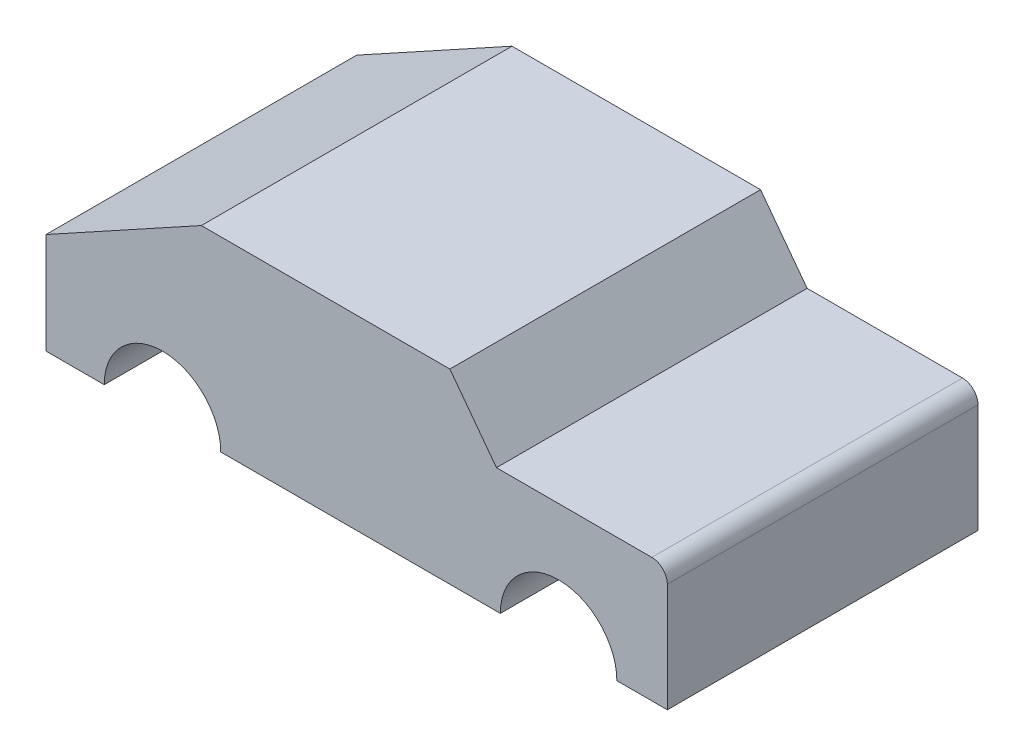
SolidWorks part; units mm, degrees
ref_plane "Front Plane" through (0, 0, 0) normal (0, 0, 1) x (1, 0, 0)
ref_plane "Top Plane" through (0, 0, 0) normal (0, 1, 0) x (1, 0, 0)
ref_plane "Right Plane" through (0, 0, 0) normal (1, 0, 0) x (0, 0, -1)
sketch "Sketch2" plane through (0, 0, 0) normal (0, 0, 1) x (1, 0, 0)
  line L0 (332.0819, 10.1189) -> (232.0819, 65.1189)
  line L2 (-67.9181, 15.1189) -> (-67.9181, -54.8811)
  line L3 (-67.9181, -54.8811) -> (-35.4181, -54.8811)
  line L4 (332.0819, 10.1189) -> (332.0819, -54.8811)
  line L5 (232.0819, 65.1189) -> (72.0819, 65.1189)
  line L6 (72.0819, 65.1189) -> (42.0819, 25.1189)
  line L7 (42.0819, 25.1189) -> (-57.9181, 25.1189)
  line L8 (39.5819, -54.8811) -> (219.5819, -54.8811)
  line L9 (294.5819, -54.8811) -> (332.0819, -54.8811)
  arc A1 (-57.9181, 25.1189) -> (-67.9181, 15.1189) centre (-57.9181, 15.1189) ccw
  arc A2 (39.5819, -54.8811) -> (-35.4181, -54.8811) centre (2.0819, -54.8811) ccw
  arc A3 (294.5819, -54.8811) -> (219.5819, -54.8811) centre (257.0819, -54.8811) ccw
  dimension "D4" = 20
  dimension "D13" = 75
  dimension "D14" = 75
  dimension "D2" = 400
  dimension "D3" = 100
  dimension "D5" = 10
  dimension "D6" = 30
  dimension "D7" = 40
  dimension "D8" = 160
  dimension "D9" = 100
  dimension "D10" = 55
  dimension "D11" = 70
  dimension "D12" = 75
extrude "Boss-Extrude1" add sketch "Sketch2" along normal blind 200
move or copy body "Body-Move/Copy1" bodies to move or copy 101 copy no rotation origin (0, 0, 0) rotation axis (0, 1, 0) rotation angle 180
sketch "Sketch9" plane through (0, 0, 0) normal (0, 0, 1) x (1, 0, 0)
  circle A0 centre (-257.0819, -54.8811) radius 37.5
  circle A1 centre (-2.0819, -54.8811) radius 37.5
sketch "Sketch10" plane through (0, -54.8811, 0) normal (0, -1, 0) x (1, 0, 0)
  line L0 (-332.0819, 0) -> (-332.0819, 50)
  dimension "D1" = 50
sketch "Sketch11" plane through (0, 0, 0) normal (0, 0, 1) x (1, 0, 0)
  circle A0 centre (57.9181, 15.1189) radius 10
